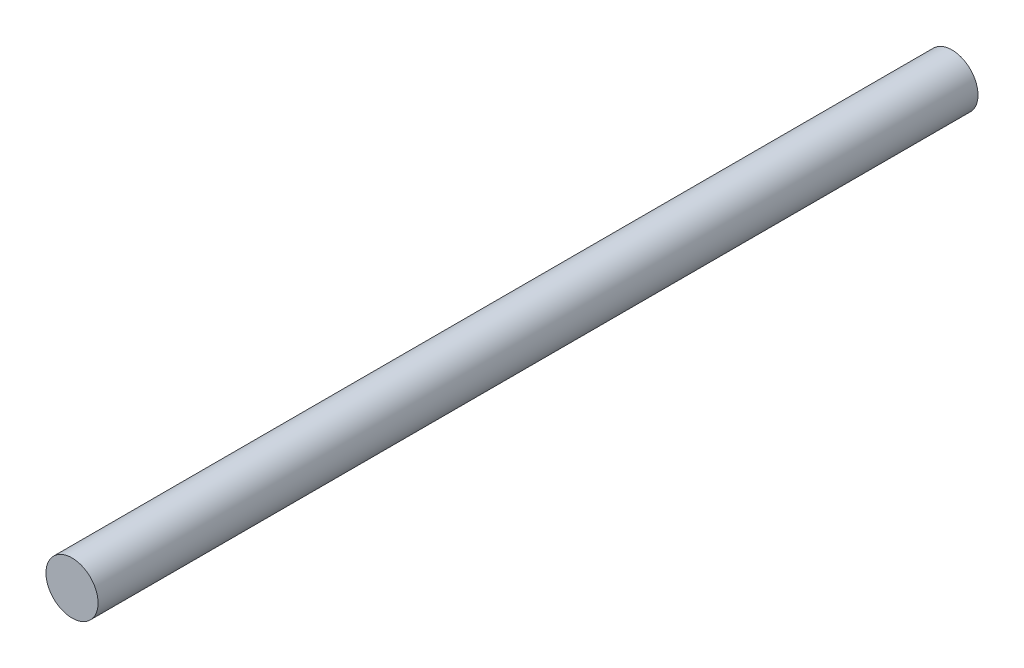
SolidWorks part; units mm, degrees
ref_plane "Front Plane" through (0, 0, 0) normal (0, 0, 1) x (1, 0, 0)
ref_plane "Top Plane" through (0, 0, 0) normal (0, 1, 0) x (1, 0, 0)
ref_plane "Right Plane" through (0, 0, 0) normal (1, 0, 0) x (0, 0, -1)
sketch "Sketch1" plane through (0, 0, 0) normal (0, 0, 1) x (1, 0, 0)
  circle A0 centre (0, 0) radius 12.5
  dimension "D1" = 25
extrude "Boss-Extrude1" add sketch "Sketch1" along normal blind 422
